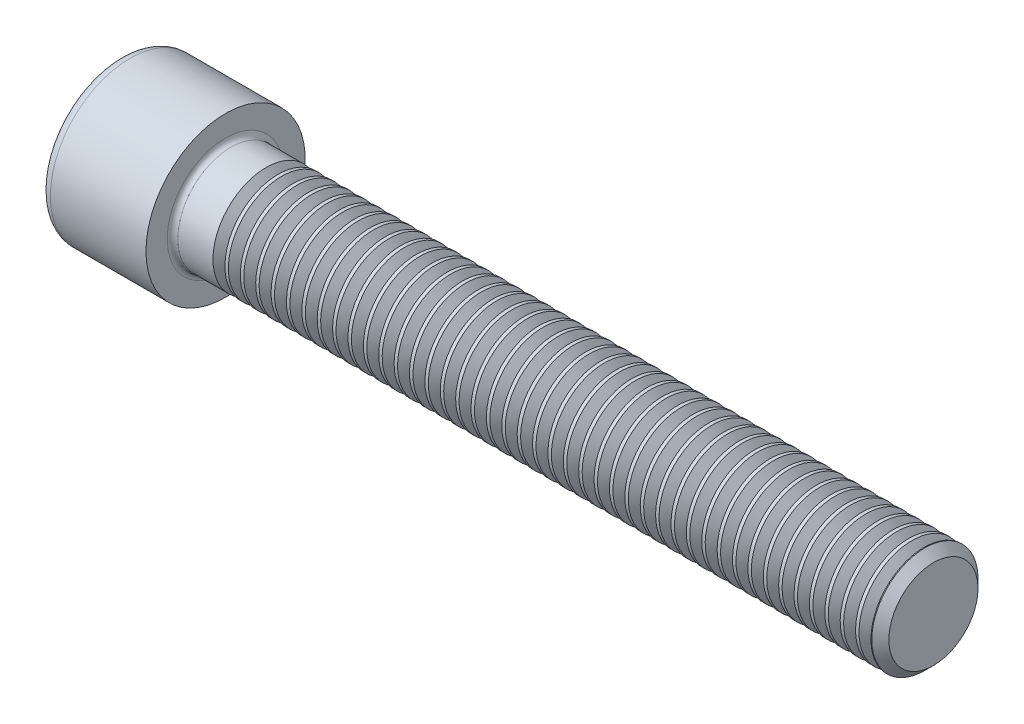
SolidWorks part; units mm, degrees
revolve "Base-Revolve" add sketch "BodySke"
sketch "BodySke" plane through (0, 0, 0) normal (0, 0, 1) x (1, 0, 0)
  line L0 (0, 0) -> (0, 9)
  line L1 (0, 9) -> (12, 9)
  line L2 (12, 9) -> (12, 6)
  line L3 (12, 6) -> (91.036, 6)
  line L4 (92, 5.036) -> (92, 0)
  line L5 (92, 0) -> (0, 0)
  line L6 (-31.75, 0) -> (127, 0) construction
  line L8 (92, 5.036) -> (91.036, 6)
  line L10 (92, -5.036) -> (91.036, -6) construction
  line L11 (13.75, 9.525) -> (13.75, 3.175) construction
  line L12 (17, 9.525) -> (17, 3.175) construction
  line L13 (12, 9.525) -> (12, 3.175) construction
cosmetic thread "ThreadCosmetic" [suppressed]
fillet "Fillet1" radius 0.6 1 edges at (12, 0, 6)
fillet "Fillet2" radius 1.2 1 edges at (0, 0, 9)
ref_plane "Plane1" through (0, 0, 0) normal (0, 0, 1) x (1, 0, 0)
ref_plane "Plane2" through (0, 0, 0) normal (0, 1, 0) x (1, 0, 0)
ref_plane "Plane3" through (0, 0, 0) normal (1, 0, 0) x (0, 0, -1)
sketch "Sketch2" plane through (0, 0, 0) normal (0, 0, 1) x (1, 0, 0)
  line L0 (0, 5.0125) -> (6, 5.0125)
  line L1 (6, 5.0125) -> (8.894, 0)
  line L2 (-31.75, 0) -> (127, 0) construction
  line L3 (8.894, 0) -> (0, 0)
  line L4 (0, 0) -> (0, 5.0125)
  line L6 (0, 0) -> (47.625, 0) construction
revolve "Hex-PreBroach" cut sketch "Sketch2" angle 360 about L6
sketch "Sketch3" plane through (0, 0, 0) normal (-1, 0, 0) x (0, 0.5, 0.866)
  line L0 (2.894, 5.0125) -> (-2.894, 5.0125)
  line L1 (-2.894, 5.0125) -> (-5.7879, 0)
  line L2 (2.894, 5.0125) -> (5.7879, 0)
  line L3 (2.894, -5.0125) -> (5.7879, 0)
  line L4 (2.894, -5.0125) -> (-2.894, -5.0125)
  line L5 (-2.894, -5.0125) -> (-5.7879, 0)
extrude "Hex" cut sketch "Sketch3" against normal blind 6
sketch "ThdSchSke" plane through (0, 0, 0) normal (0, 0, 1) x (1, 0, 0)
  line L0 (17.25, -5.036) -> (16.575, -6)
  line L1 (17.25, -5.036) -> (17.925, -6)
  line L2 (17.925, -6) -> (17.925, -7.5)
  line L3 (-3.175, 0) -> (5.1513, 0) construction
  line L4 (0, 7.8) -> (0, -7.8) construction
  line L5 (17.925, -7.5) -> (16.575, -7.5)
  line L6 (16.575, -7.5) -> (16.575, -6)
revolve "ThreadSchematic" cut sketch "ThdSchSke" angle 360 about L3
pattern_linear "ThdSchPat" count 43 spacing 1.7384 along (1, 0, 0) of "ThreadSchematic"
equation "\"D2@Sketch3\" = \"Hex_size@Sketch3\" / 2"
equation "\"D1@Sketch3\" = \"Hex_size@Sketch3\" / 2"
equation "\"D1@Sketch2\" = \"Hex_size@Sketch3\" / 2"
equation "\"Thread_minor@ThreadCosmetic\"  =  \"Minor_dia@BodySke\""
equation "\"Depth@Sketch2\" =  \"Key_eng@Hex\""
equation "\"Thread_length@ThreadCosmetic\" = ((sgn( (\"Length@BodySke\" - \"Advance@BodySke\" * 3.0) - \"Thread_nom@BodySke\" )-1)*( (\"Length@BodySke\" - \"Advance@BodySke\" * 3.0) - \"Thread_nom@BodySke\" ))/-2+ \"Thread_nom@BodySke\""
equation "\"Thread_minor@ThdSchSke\" = \"Minor_dia@BodySke\""
equation "\"Diameter@ThdSchSke\" = \"Diameter@BodySke\""
equation "\"Overcut@ThdSchSke\" = \"Diameter@BodySke\" * 1.25"
equation "\"Start@ThdSchSke\" = \"Head_ht@BodySke\" + \"Length@BodySke\" - \"Thread_length@ThreadCosmetic\"  '---Non-countersunk---"
equation "\"Num_threads@ThdSchPat\" = int( \"Thread_length@ThreadCosmetic\" / \"Advance@BodySke\" + 0.999 )  + 1"
equation "\"Advance@ThdSchPat\" = \"Thread_length@ThreadCosmetic\" /  (\"Num_threads@ThdSchPat\" - 1) 'relax it"
equation "\"Num_threads@ThdSchPat\" = \"Num_threads@ThdSchPat\" - sgn( \"Num_threads@ThdSchPat\" - 1) '---chamfered tips only---"
